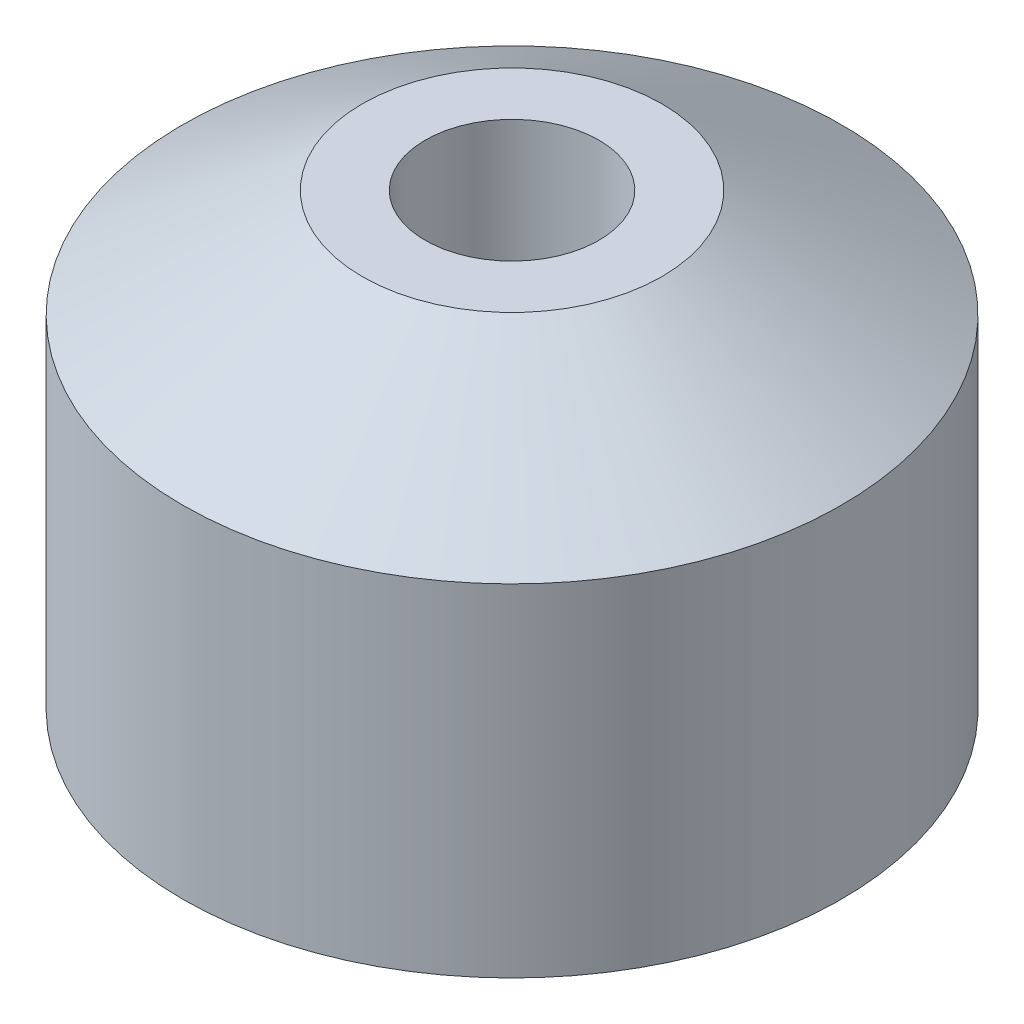
SolidWorks part; units mm, degrees
ref_plane "Front Plane" through (0, 0, 0) normal (0, 0, 1) x (1, 0, 0)
ref_plane "Top Plane" through (0, 0, 0) normal (0, 1, 0) x (1, 0, 0)
ref_plane "Right Plane" through (0, 0, 0) normal (1, 0, 0) x (0, 0, -1)
sketch "Sketch1" plane through (0, 0, 0) normal (1, 0, 0) x (0, 0, -1)
  line L0 (-5.5, 5.6974) -> (-5.5, 0)
  line L1 (-5.5, 0) -> (0, 0)
  line L4 (0, 7.5) -> (-2.5, 7.5)
  line L5 (-2.5, 7.5) -> (-5.5, 5.6974)
  line L6 (0, 7.5) -> (0, 0) construction
  line L7 (0, 7.5) -> (0, 0)
  dimension "D1" = 7.5
  dimension "D2" = 11
  dimension "D3" = 5
  dimension "D4" = 121
revolve "Revolve1" add sketch "Sketch1" angle 360 about L6
hole_wizard "CBORE for M2.5 SHCS1" positions "Sketch2" profile "Sketch4" counterbore size "M2.5" standard "ANSI Metric" end condition through all
sketch "Sketch2" plane through (0, 0, 0) normal (0, -1, 0) x (-1, 0, 0)
  point P0 (0, 0)
sketch "Sketch4" plane through (0, 0, 0) normal (1, 0, 0) x (0, 0, -1)
  line L0 (0, 0) -> (0, 7.5)
  line L1 (0, 7.5) -> (1.45, 7.5)
  line L3 (1.45, 7.5) -> (1.45, 2.6)
  line L4 (1.45, 2.6) -> (2.75, 2.6)
  line L5 (2.75, 2.6) -> (2.75, 0)
  line L7 (2.75, 0) -> (0, 0)
  line L11 (0, -6.35) -> (0, 107.95) construction
  dimension "Thru Hole Dia." = 2.9
  dimension "Thru Hole Depth" = 7.5
  dimension "C'Bore Dia." = 5.5
  dimension "C'Bore Depth" = 2.6
